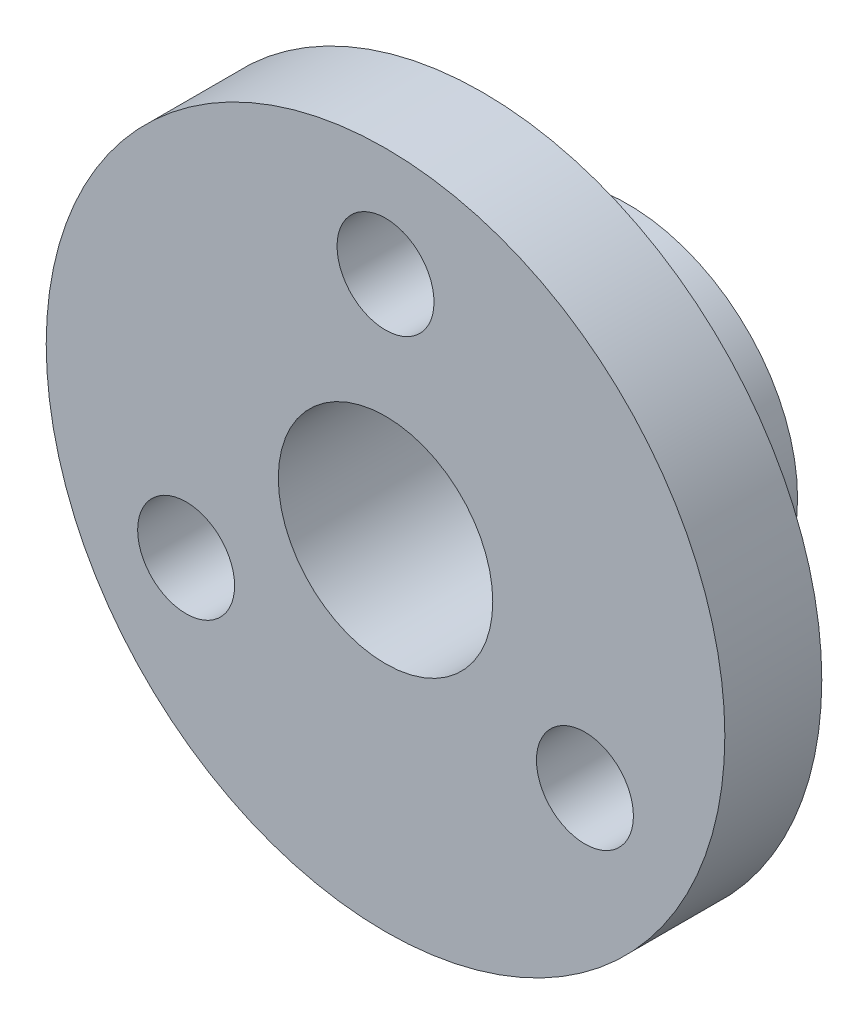
SolidWorks part; units mm, degrees
material "ABS"
ref_plane "Ön Düzlem" through (0, 0, 0) normal (0, 0, 1) x (1, 0, 0)
ref_plane "Üst Düzlem" through (0, 0, 0) normal (0, 1, 0) x (1, 0, 0)
ref_plane "Sağ Düzlem" through (0, 0, 0) normal (1, 0, 0) x (0, 0, -1)
sketch "Çizim1" plane through (0, 0, 0) normal (0, 0, 1) x (1, 0, 0)
  circle A0 centre (-30.7119, -38.9048) radius 2.2124
  circle A1 centre (-30.7119, -38.9048) radius 7
extrude "Yükseklik-Ekstrüzyon1" add sketch "Çizim1" along normal blind 2
sketch "Çizim2" plane through (0, 0, 2) normal (0, 0, 1) x (1, 0, 0)
  circle A0 centre (-30.7119, -38.9048) radius 2.2124
  circle A1 centre (-30.7119, -38.9048) radius 3.5
extrude "Yükseklik-Ekstrüzyon2" add sketch "Çizim2" against normal blind 5
sketch "Çizim3" plane through (0, 0, 0) normal (0, 0, -1) x (-1, 0, 0)
  circle A0 centre (30.7119, -38.9048) radius 4.75 construction
  circle A1 centre (30.7119, -34.1548) radius 1
  circle A2 centre (34.8255, -41.2798) radius 1
  circle A3 centre (26.5983, -41.2798) radius 1
  point P11 (30.7119, -38.9048)
  dimension "D1" = 3
extrude "Kes-Ekstrüzyon1" cut sketch "Çizim3" against normal blind 5
